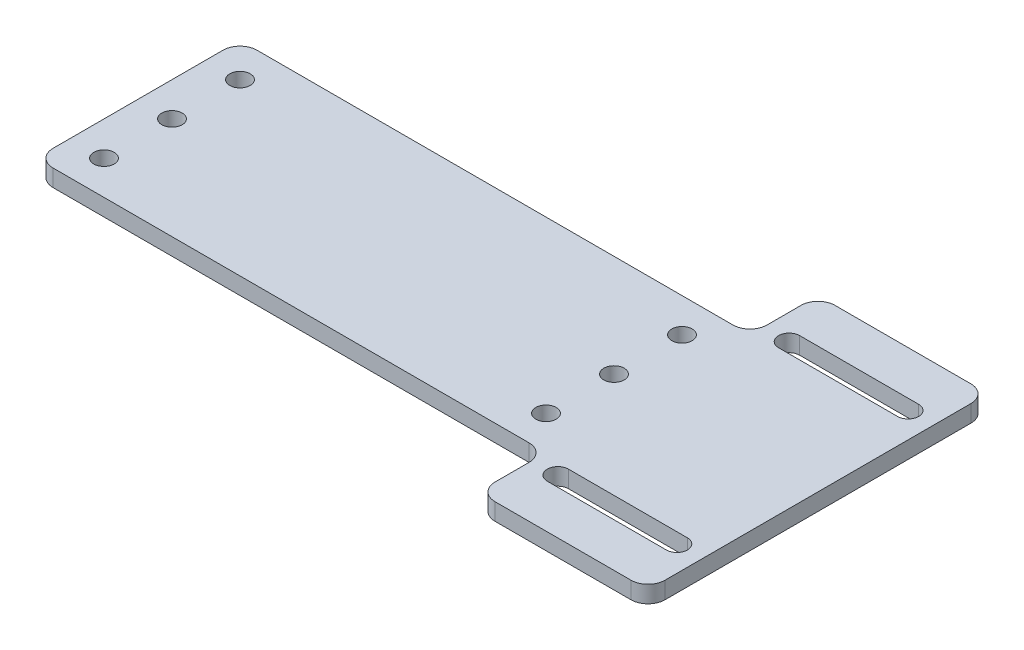
SolidWorks part; units mm, degrees
ref_plane "Front Plane" through (0, 0, 0) normal (0, 0, 1) x (1, 0, 0)
ref_plane "Top Plane" through (0, 0, 0) normal (0, 1, 0) x (1, 0, 0)
ref_plane "Right Plane" through (0, 0, 0) normal (1, 0, 0) x (0, 0, -1)
sketch "Sketch1" plane through (0, 0, 0) normal (0, 1, 0) x (1, 0, 0)
  line L1 (-100, -30) -> (100, -30)
  line L2 (-100, -30) -> (-100, 30)
  line L3 (-100, 30) -> (100, 30)
  line L4 (100, -30) -> (100, 30)
  line L5 (0, 30) -> (0, -30) construction
  line L6 (-100, 0) -> (100, 0) construction
  point P0 (0, 0)
  dimension "D1" = 60
  dimension "D2" = 200
extrude "Boss-Extrude1" add sketch "Sketch1" along normal blind 5
sketch "Sketch2" plane through (0, 5, 0) normal (0, 1, 0) x (1, 0, 0)
  line L0 (50, 30) -> (50, -30) construction
  line L1 (100, 30) -> (-100, 30) construction
  line L2 (-100, -30) -> (100, -30) construction
  line L3 (-100, 30) -> (-100, -30) construction
  line L4 (50, 0) -> (-100, 0) construction
  line L6 (-90, -20) -> (40, -20) construction
  line L7 (-90, -20) -> (-90, 20) construction
  line L8 (-90, 20) -> (40, 20) construction
  line L9 (40, -20) -> (40, 20) construction
  line L10 (-25, 20) -> (-25, -20) construction
  line L11 (-90, 0) -> (40, 0) construction
  circle A0 centre (-90, 20) radius 3
  circle A1 centre (-90, -20) radius 3
  circle A2 centre (40, -20) radius 3
  circle A3 centre (40, 20) radius 3
  circle A4 centre (-90, 0) radius 3
  circle A5 centre (40, 0) radius 3
  point P10 (-25, 0)
  dimension "D2" = 6
  dimension "D1" = 150
  dimension "D3" = 40
  dimension "D4" = 130
extrude "Cut-Extrude1" cut sketch "Sketch2" against normal through all
sketch "Sketch3" plane through (0, 0, 0) normal (0, 1, 0) x (1, 0, 0)
  line L0 (50, -50) -> (100, -50)
  line L1 (50, -50) -> (50, 50)
  line L2 (100, -50) -> (100, 50)
  line L3 (50, 50) -> (100, 50)
  line L4 (50, -50) -> (100, 50) construction
  line L5 (100, -50) -> (50, 50) construction
  line L6 (100, -30) -> (100, 30) construction
  line L7 (0, 0) -> (100, 0) construction
  circle A0 centre (40, 20) radius 3 construction
  point P1 (75, 0)
  point P12 (0, 0)
  dimension "D1" = 10
  dimension "D2" = 100
extrude "Boss-Extrude2" add sketch "Sketch3" along normal up to surface (5 mm away) up to face at (-90, 5, 23)
sketch "Sketch4" plane through (0, 5, 0) normal (0, 1, 0) x (1, 0, 0)
  line L0 (0, 0) -> (100, 0) construction
  line L1 (100, -50) -> (100, 50) construction
  line L2 (75, 50) -> (75, -50) construction
  line L3 (50, 50) -> (100, 50) construction
  line L4 (100, -50) -> (50, -50) construction
  line L5 (57.5, -34.005) -> (92.5, -34.005) construction
  line L6 (57.5, -30.905) -> (92.5, -30.905)
  line L7 (57.5, -37.105) -> (92.5, -37.105)
  arc A0 (57.5, -30.905) -> (57.5, -37.105) centre (57.5, -34.005) ccw
  arc A1 (92.5, -37.105) -> (92.5, -30.905) centre (92.5, -34.005) ccw
  point P13 (75, -34.005)
  dimension "D1" = 3.1
  dimension "D2" = 35
  dimension "D3" = 34.005
extrude "Cut-Extrude2" cut sketch "Sketch4" against normal through all
mirror "Mirror1" about plane through (0, 0, 0) normal (0, 0, 1) of "Cut-Extrude2"
fillet "Fillet1" radius 5 8 edges at (-100, 2.5, 30) (-100, 2.5, -30) (100, 2.5, -50) (50, 2.5, -50) (50, 2.5, -30) (100, 2.5, 50) (50, 2.5, 50) (50, 2.5, 30)
